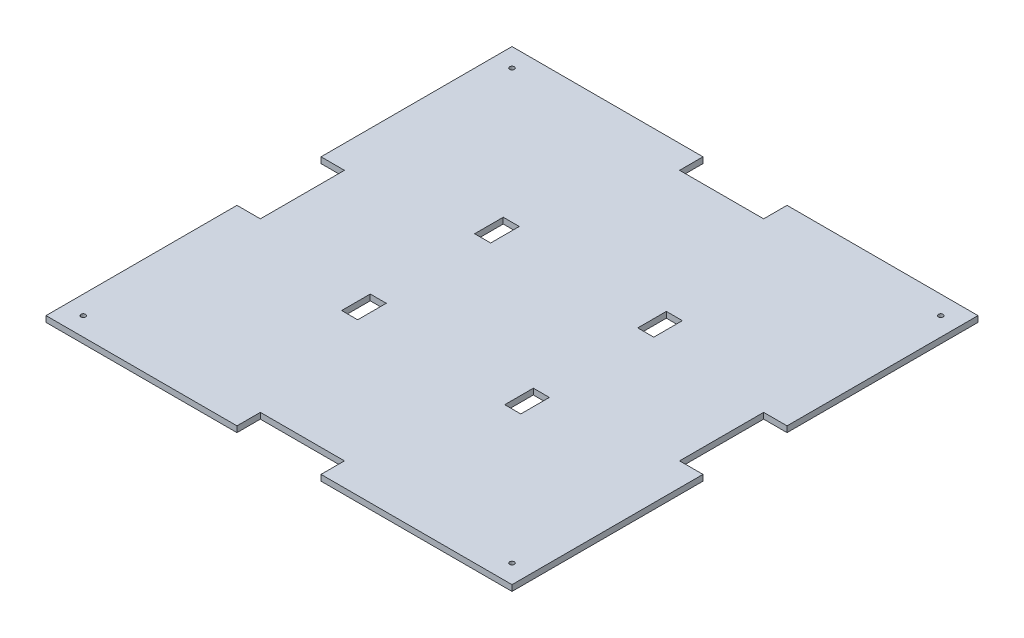
SolidWorks part; units mm, degrees
ref_plane "Front Plane" through (0, 0, 0) normal (0, 0, 1) x (1, 0, 0)
ref_plane "Top Plane" through (0, 0, 0) normal (0, 1, 0) x (1, 0, 0)
ref_plane "Right Plane" through (0, 0, 0) normal (1, 0, 0) x (0, 0, -1)
sketch "Sketch2" plane through (0, 0, 0) normal (0, 1, 0) x (1, 0, 0)
  line L1 (-125, -125) -> (125, -125)
  line L2 (-125, -125) -> (-125, 125)
  line L3 (-125, 125) -> (125, 125)
  line L4 (125, -125) -> (125, 125)
  line L5 (-125, -125) -> (125, 125) construction
  line L6 (-125, 125) -> (125, -125) construction
  point P0 (0, 0)
  dimension "D1" = 250
  dimension "D2" = 250
extrude "Boss-Extrude1" add sketch "Sketch2" along normal blind 3.175
sketch "Sketch3" plane through (0, 3.175, 0) normal (0, 1, 0) x (1, 0, 0)
  line L0 (-125, 0) -> (125, 0) construction
  line L1 (-125, 125) -> (-125, -125) construction
  line L2 (125, -125) -> (125, 125) construction
  line L3 (-43.75, 125) -> (-43.75, -125) construction
  line L4 (125, 125) -> (-125, 125) construction
  line L5 (-125, -125) -> (125, -125) construction
  line L6 (0, 125) -> (0, -125) construction
  line L11 (-48.05, 28) -> (-39.45, 28)
  line L12 (-48.05, 28) -> (-48.05, 43.35)
  line L13 (-48.05, 43.35) -> (-39.45, 43.35)
  line L14 (-39.45, 28) -> (-39.45, 43.35)
  line L15 (-48.05, 28) -> (-39.45, 43.35) construction
  line L16 (-48.05, 43.35) -> (-39.45, 28) construction
  line L21 (-48.05, -43.35) -> (-39.45, -43.35)
  line L22 (-48.05, -43.35) -> (-48.05, -28)
  line L23 (-48.05, -28) -> (-39.45, -28)
  line L24 (-39.45, -43.35) -> (-39.45, -28)
  line L25 (-48.05, -43.35) -> (-39.45, -28) construction
  line L26 (-48.05, -28) -> (-39.45, -43.35) construction
  line L27 (48.05, -28) -> (39.45, -28)
  line L28 (39.45, -43.35) -> (39.45, -28)
  line L29 (48.05, -43.35) -> (39.45, -43.35)
  line L30 (48.05, -43.35) -> (48.05, -28)
  line L31 (48.05, 43.35) -> (39.45, 43.35)
  line L32 (39.45, 28) -> (39.45, 43.35)
  line L33 (48.05, 28) -> (39.45, 28)
  line L34 (48.05, 28) -> (48.05, 43.35)
  point P12 (-43.75, 35.675)
  point P17 (-43.75, -35.675)
  dimension "D1" = 43.75
  dimension "D2" = 8.6
  dimension "D3" = 15.35
  dimension "D4" = 56
  dimension "D5" = 28
extrude "Cut-Extrude1" cut sketch "Sketch3" against normal blind 10
sketch "Sketch4" plane through (0, 3.175, 0) normal (0, 1, 0) x (1, 0, 0)
  line L0 (0, 125) -> (0, -125) construction
  line L1 (125, 125) -> (-125, 125) construction
  line L2 (-125, -125) -> (125, -125) construction
  line L3 (-125, 0) -> (125, 0) construction
  line L4 (-125, 125) -> (-125, -125) construction
  line L5 (125, -125) -> (125, 125) construction
  line L7 (-22.55, 137.55) -> (22.55, 137.55)
  line L8 (-22.55, 137.55) -> (-22.55, 112.45)
  line L9 (-22.55, 112.45) -> (22.55, 112.45)
  line L10 (22.55, 137.55) -> (22.55, 112.45)
  line L11 (-22.55, 137.55) -> (22.55, 112.45) construction
  line L12 (-22.55, 112.45) -> (22.55, 137.55) construction
  line L28 (137.55, 22.55) -> (112.45, 22.55)
  line L29 (137.55, 22.55) -> (137.55, -22.55)
  line L30 (137.55, -22.55) -> (112.45, -22.55)
  line L31 (112.45, 22.55) -> (112.45, -22.55)
  line L32 (22.55, -137.55) -> (22.55, -112.45)
  line L33 (22.55, -137.55) -> (-22.55, -137.55)
  line L34 (-22.55, -137.55) -> (-22.55, -112.45)
  line L35 (22.55, -112.45) -> (-22.55, -112.45)
  line L36 (-137.55, -22.55) -> (-112.45, -22.55)
  line L37 (-137.55, -22.55) -> (-137.55, 22.55)
  line L38 (-137.55, 22.55) -> (-112.45, 22.55)
  line L39 (-112.45, -22.55) -> (-112.45, 22.55)
  point P31 (-25, 25)
  point P32 (0, 0)
  dimension "D1" = 25.1
  dimension "D2" = 45.1
  dimension "D3" = 4
extrude "Cut-Extrude2" cut sketch "Sketch4" against normal blind 10
hole_wizard "M3 Tapped Hole1" positions "Sketch5" profile "Sketch6" tap size "M3" standard "ISO" end condition through all
sketch "Sketch5" plane through (0, 3.175, 0) normal (0, 1, 0) x (1, 0, 0)
  line L0 (-22.55, 125) -> (-125, 125) construction
  line L1 (-125, 125) -> (-125, 22.55) construction
  point P0 (-115, 115)
  dimension "D1" = 10
  dimension "D2" = 10
sketch "Sketch6" plane through (-115, 3.175, -115) normal (1, 0, 0) x (0, 0, 1)
  line L0 (0, 0) -> (0, 3.175)
  line L1 (0, 3.175) -> (1.25, 3.175)
  line L2 (1.25, 3.175) -> (1.25, 0)
  line L5 (1.25, 0) -> (0, 0)
  line L11 (0, -6.35) -> (0, 107.95) construction
  dimension "Thru Tap Drill Dia." = 2.5
  dimension "Thru Tap Drill Depth" = 3.175
cosmetic thread "Hole Thread1" parameters "D2"=3
hole_wizard "M3 Tapped Hole2" positions "Sketch7" profile "Sketch8" tap size "M3" standard "ISO" end condition through all
sketch "Sketch7" plane through (0, 3.175, 0) normal (0, 1, 0) x (1, 0, 0)
  line L0 (-125, -125) -> (-22.55, -125) construction
  line L1 (-125, -22.55) -> (-125, -125) construction
  line L2 (125, -125) -> (125, -22.55) construction
  line L3 (22.55, -125) -> (125, -125) construction
  line L4 (125, 22.55) -> (125, 125) construction
  line L5 (125, 125) -> (22.55, 125) construction
  point P0 (115, 115)
  point P2 (115, -115)
  point P4 (-115, -115)
  dimension "D1" = 10
  dimension "D2" = 10
  dimension "D3" = 10
  dimension "D4" = 10
  dimension "D5" = 10
  dimension "D6" = 10
sketch "Sketch8" plane through (115, 3.175, -115) normal (1, 0, 0) x (0, 0, 1)
  line L0 (0, 0) -> (0, 3.175)
  line L1 (0, 3.175) -> (1.25, 3.175)
  line L2 (1.25, 3.175) -> (1.25, 0)
  line L5 (1.25, 0) -> (0, 0)
  line L11 (0, -6.35) -> (0, 107.95) construction
  dimension "Thru Tap Drill Dia." = 2.5
  dimension "Thru Tap Drill Depth" = 3.175
cosmetic thread "Hole Thread2" parameters "D2"=3
cosmetic thread "Hole Thread3" parameters "D2"=3
cosmetic thread "Hole Thread4" parameters "D2"=3
